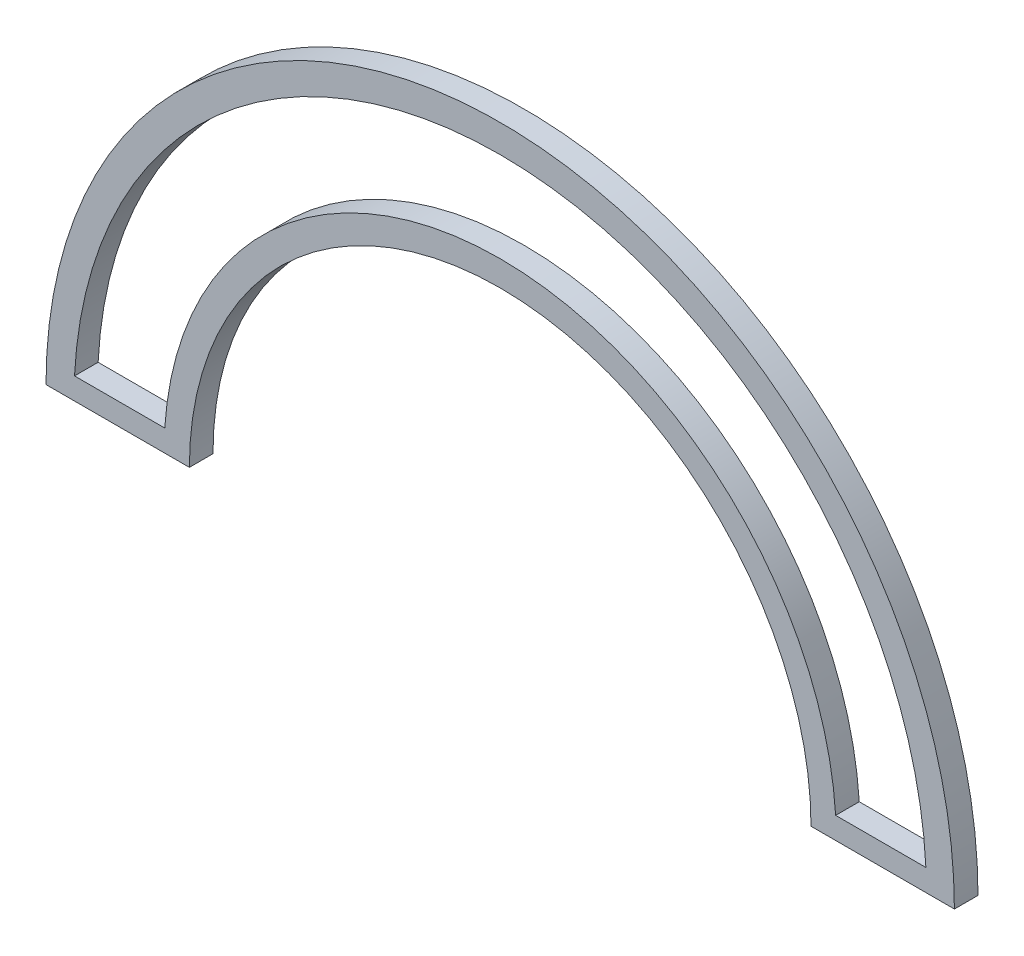
SolidWorks part; units mm, degrees
ref_plane "Front Plane" through (0, 0, 0) normal (0, 0, 1) x (1, 0, 0)
ref_plane "Top Plane" through (0, 0, 0) normal (0, 1, 0) x (1, 0, 0)
ref_plane "Right Plane" through (0, 0, 0) normal (1, 0, 0) x (0, 0, -1)
sketch "Sketch1" plane through (0, 0, 0) normal (0, 0, 1) x (1, 0, 0)
  line L2 (-96.2196, 0) -> (-65.8461, 0)
  line L3 (65.8461, 0) -> (96.2196, 0)
  line L4 (-90.1815, 4.6108) -> (-71.0625, 4.6108)
  line L6 (71.0625, 4.6108) -> (90.1815, 4.6108)
  arc A2 (96.2196, 0) -> (-96.2196, 0) centre (0, 0) ccw
  arc A3 (65.8461, 0) -> (-65.8461, 0) centre (0, 0) ccw
  arc A4 (90.1815, 4.6108) -> (-90.1815, 4.6108) centre (0, 0) ccw
  arc A5 (71.0625, 4.6108) -> (-71.0625, 4.6108) centre (0, 0) ccw
  point P0 (0, 0)
extrude "Boss-Extrude1" add sketch "Sketch1" along normal blind 5
sketch "Sketch2" plane through (0, 0, 5) normal (0, 0, 1) x (1, 0, 0)
  line L0 (-90.1815, 4.6108) -> (-71.0625, 4.6108)
  line L1 (-90.1815, 4.6108) -> (-71.0625, 4.6108) construction
  line L2 (71.0625, 4.6108) -> (90.1815, 4.6108) construction
  line L3 (71.0625, 4.6108) -> (90.1815, 4.6108)
  arc A0 (90.1815, 4.6108) -> (-90.1815, 4.6108) centre (0, 0) ccw
  arc A1 (71.0625, 4.6108) -> (-71.0625, 4.6108) centre (0, 0) ccw
  point P0 (0, 0)
